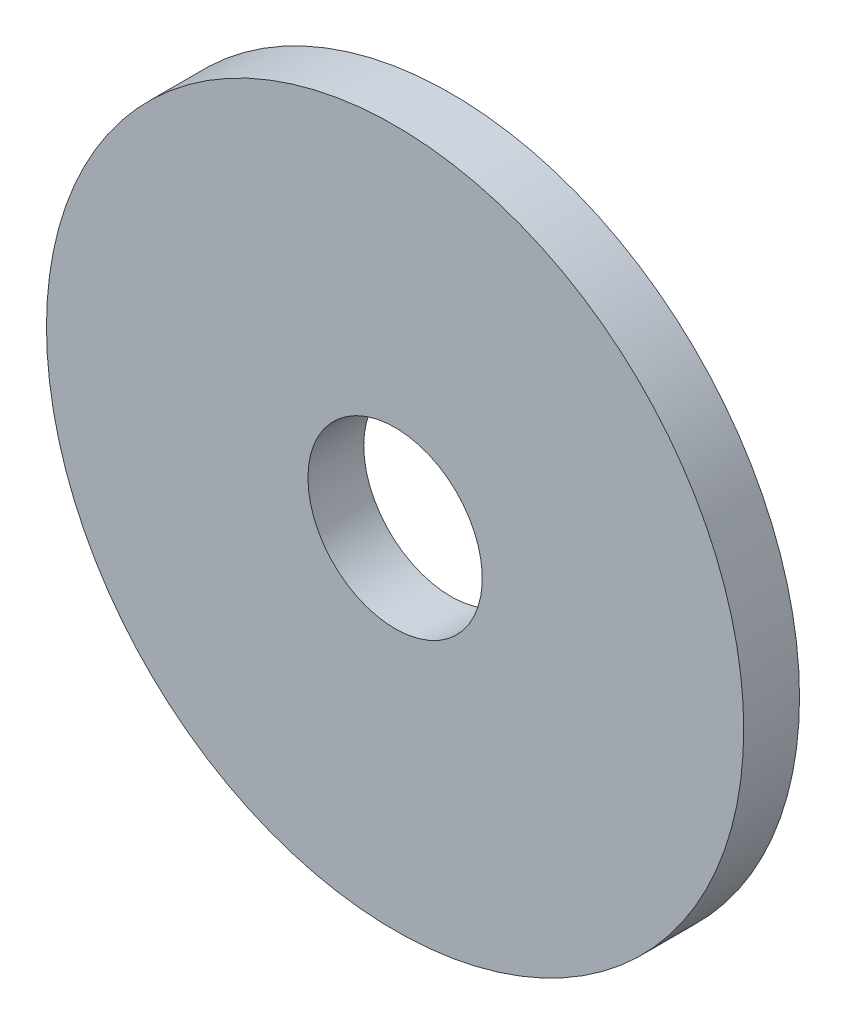
SolidWorks part; units mm, degrees
ref_plane "Plan de face" through (0, 0, 0) normal (0, 0, 1) x (1, 0, 0)
ref_plane "Plan de dessus" through (0, 0, 0) normal (0, 1, 0) x (1, 0, 0)
ref_plane "Plan de droite" through (0, 0, 0) normal (1, 0, 0) x (0, 0, -1)
sketch "Esquisse1" plane through (0, 0, 0) normal (0, 0, 1) x (1, 0, 0)
  circle A0 centre (0, 0) radius 12.5
  dimension "D1" = 25
extrude "Boss.-Extru.1" add sketch "Esquisse1" along normal blind 2
sketch "Esquisse2" plane through (0, 0, 0) normal (0, 0, -1) x (-1, 0, 0)
  circle A0 centre (0, 0) radius 3.125
  dimension "D1" = 6.25
extrude "Enlèv. mat.-Extru.1" cut sketch "Esquisse2" against normal through all
